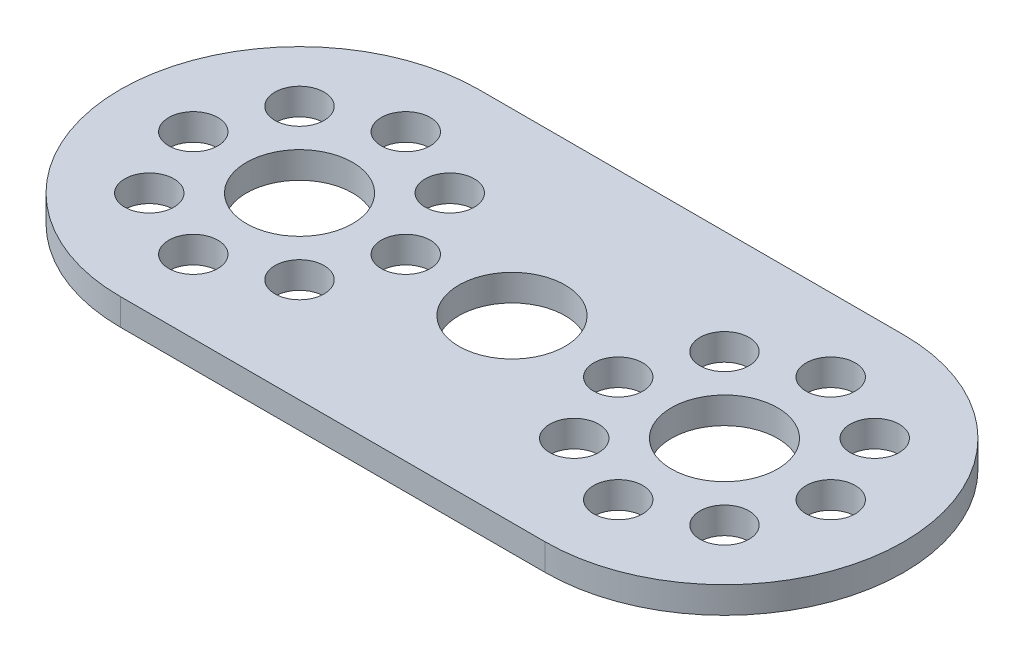
SolidWorks part; units mm, degrees
material "2024 Alloy"
ref_plane "Front Plane" through (0, 0, 0) normal (0, 0, 1) x (1, 0, 0)
ref_plane "Top Plane" through (0, 0, 0) normal (0, 1, 0) x (1, 0, 0)
ref_plane "Right Plane" through (0, 0, 0) normal (1, 0, 0) x (0, 0, -1)
sketch "Sketch1" plane through (0, 0, 0) normal (0, 1, 0) x (1, 0, 0)
  line L0 (0, 0) -> (0, 14.6056) construction
  line L1 (0, 0) -> (16, 0) construction
  line L3 (-16, 13.5) -> (16, 13.5)
  line L4 (-16, 13.5) -> (-16, -13.5) construction
  line L5 (-16, -13.5) -> (16, -13.5)
  line L6 (16, 13.5) -> (16, -13.5) construction
  circle A0 centre (0, 0) radius 4
  circle A1 centre (16, 0) radius 4
  circle A3 centre (8, 0) radius 1.85
  circle A4 centre (10.3431, 5.6569) radius 1.85
  circle A5 centre (16, 8) radius 1.85
  circle A6 centre (21.6569, 5.6569) radius 1.85
  circle A7 centre (24, 0) radius 1.85
  circle A8 centre (21.6569, -5.6569) radius 1.85
  circle A9 centre (16, -8) radius 1.85
  circle A10 centre (10.3431, -5.6569) radius 1.85
  circle A11 centre (-10.3431, -5.6569) radius 1.85
  circle A12 centre (-16, -8) radius 1.85
  circle A13 centre (-21.6569, -5.6569) radius 1.85
  circle A14 centre (-24, 0) radius 1.85
  circle A15 centre (-21.6569, 5.6569) radius 1.85
  circle A16 centre (-16, 8) radius 1.85
  circle A17 centre (-10.3431, 5.6569) radius 1.85
  circle A18 centre (-8, 0) radius 1.85
  circle A19 centre (-16, 0) radius 4
  arc A20 (-16, 13.5) -> (-16, -13.5) centre (-16, 0) ccw
  arc A21 (16, 13.5) -> (16, -13.5) centre (16, 0) cw
  point P5 (-16, 0)
  point P26 (16, 0)
  dimension "D1" = 8
  dimension "D3" = 3.7
  dimension "D2" = 16
  dimension "D5" = 27
  dimension "D4" = 8
extrude "Boss-Extrude1" add sketch "Sketch1" along normal blind 2
